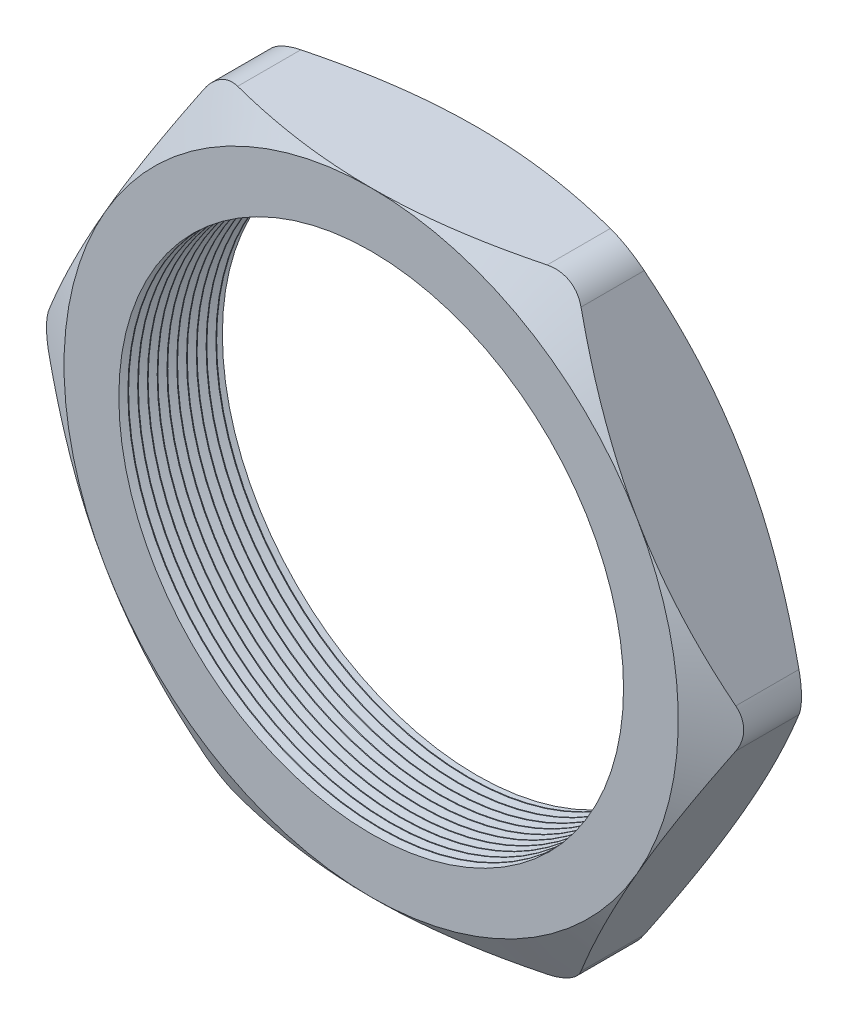
SolidWorks part; units mm, degrees
ref_plane "Front Plane" through (0, 0, 0) normal (0, 0, 1) x (1, 0, 0)
ref_plane "Top Plane" through (0, 0, 0) normal (0, 1, 0) x (1, 0, 0)
ref_plane "Right Plane" through (0, 0, 0) normal (1, 0, 0) x (0, 0, -1)
sketch "Sketch1" plane through (0, 0, 0) normal (0, 0, 1) x (1, 0, 0)
  line L1 (-23.0236, 0) -> (-11.5118, -19.939)
  line L2 (-11.5118, -19.939) -> (11.5118, -19.939)
  line L3 (11.5118, -19.939) -> (23.0236, 0)
  line L4 (23.0236, 0) -> (11.5118, 19.939)
  line L5 (11.5118, 19.939) -> (-11.5118, 19.939)
  line L6 (-11.5118, 19.939) -> (-23.0236, 0)
  circle A0 centre (0, 0) radius 19.939 construction
  circle A1 centre (0, 0) radius 16.383
  dimension "TS" = 32.766
  dimension "H" = 39.878
extrude "Extrude1" add sketch "Sketch1" along normal blind 6.858
sketch "Sketch2" plane through (0, 0, 6.858) normal (0, 0, 1) x (1, 0, 0)
  line L0 (11.5118, 19.939) -> (-11.5118, 19.939) construction
  circle A0 centre (0, 0) radius 19.939
extrude "Cut-Extrude1" cut sketch "Sketch2" against normal through all draft 60 flip side to cut
sketch "Sketch3" plane through (0, 0, 0) normal (0, 0, -1) x (-1, 0, 0)
  line L0 (-11.5118, 19.939) -> (11.5118, 19.939) construction
  circle A0 centre (0, 0) radius 19.939
extrude "Cut-Extrude2" cut sketch "Sketch3" against normal through all draft 60 flip side to cut
fillet "Fillet1" radius 2.54 6 edges at (23.0236, 0, 3.429) (11.5118, -19.939, 3.429) (-11.5118, -19.939, 3.429) (-23.0236, 0, 3.429) (-11.5118, 19.939, 3.429) (11.5118, 19.939, 3.429)
sketch "Sketch4" plane through (0, 0, 0) normal (0, 1, 0) x (1, 0, 0)
  line L0 (-16.383, -6.858) -> (-16.383, -6.2714)
  line L1 (-16.383, 0) -> (-16.383, -6.858) construction
  line L2 (-16.383, -6.2714) -> (-16.891, -6.5647)
  line L3 (-16.891, -6.5647) -> (-16.383, -6.858)
  dimension "D1" = 60
  dimension "D2" = 60
  dimension "D3" = 0.508
revolve "Cut-Revolve1" cut sketch "Sketch4" angle 360 about axis through (0, 0, 0) along (0, 0, 1)
pattern_linear "LPattern1" count 11 spacing 0.635 along (0, 0, -1) of "Cut-Revolve1"
